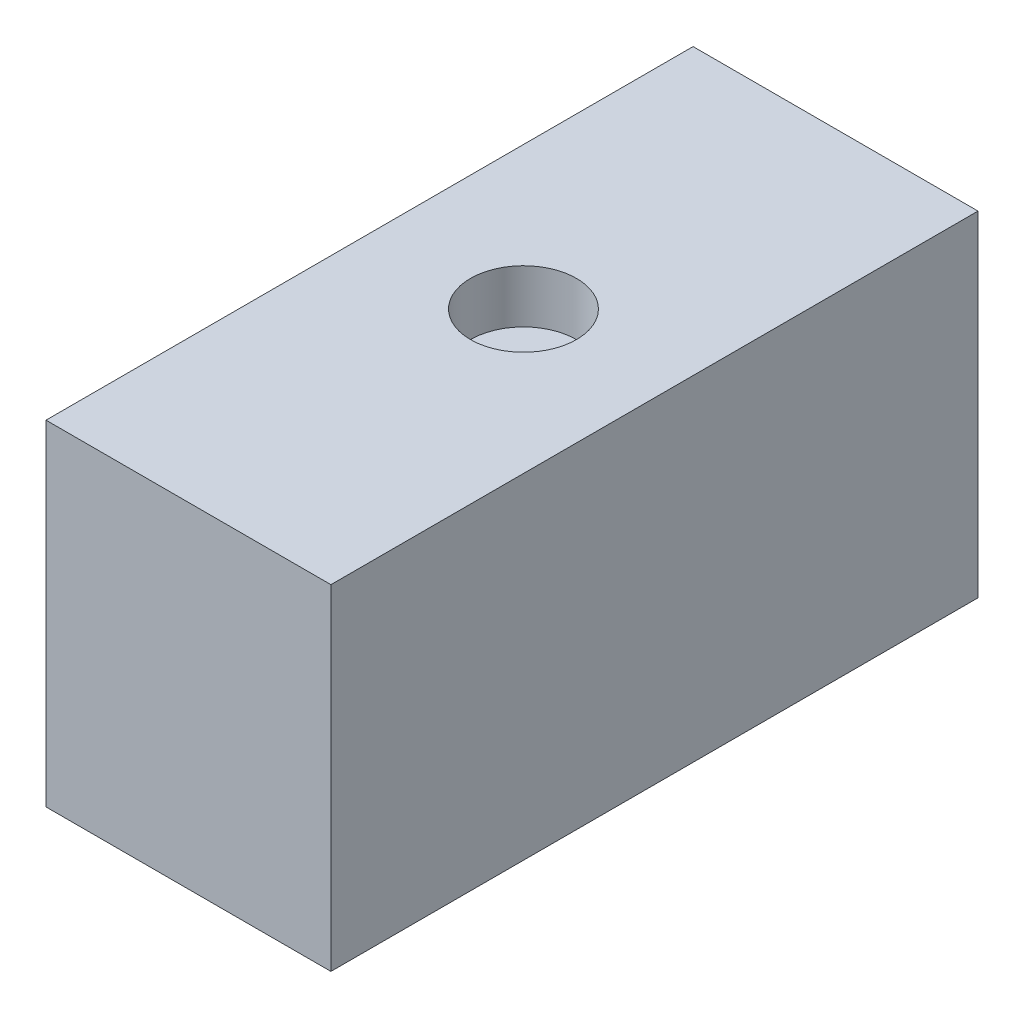
SolidWorks part; units mm, degrees
ref_plane "Front Plane" through (0, 0, 0) normal (0, 0, 1) x (1, 0, 0)
ref_plane "Top Plane" through (0, 0, 0) normal (0, 1, 0) x (1, 0, 0)
ref_plane "Right Plane" through (0, 0, 0) normal (1, 0, 0) x (0, 0, -1)
sketch "Sketch1" plane through (0, 0, 0) normal (0, 1, 0) x (1, 0, 0)
  line L1 (0, 0) -> (136.4996, 0)
  line L2 (0, 0) -> (0, 310.007)
  line L3 (0, 310.007) -> (136.4996, 310.007)
  line L4 (136.4996, 0) -> (136.4996, 310.007)
extrude "Boss-Extrude1" add sketch "Sketch1" along normal blind 160.4772
sketch "Sketch4" plane through (0, 160.4772, 0) normal (0, 1, 0) x (1, 0, 0)
  circle A0 centre (68.2498, 160.5026) radius 25.4
extrude "Cut-Extrude1" cut sketch "Sketch4" against normal blind 25.4
